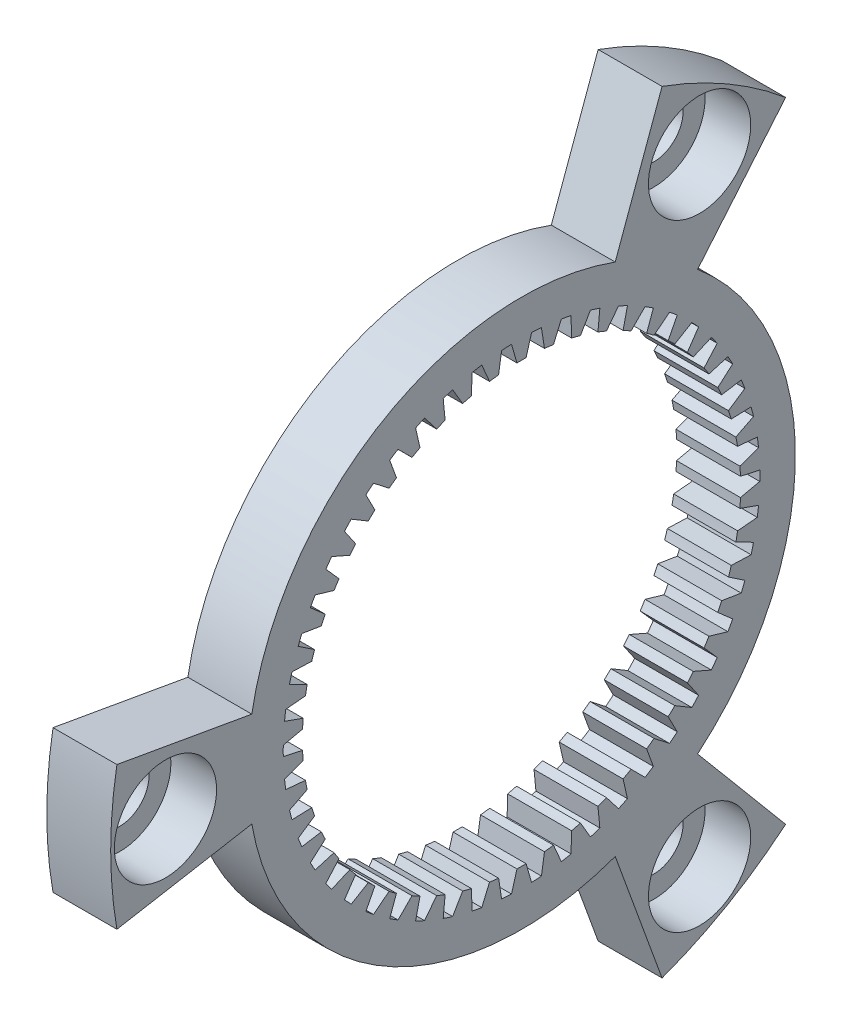
SolidWorks part; units mm, degrees
material "Plain Carbon Steel"
ref_plane "Front Plane" through (0, 0, 0) normal (0, 0, 1) x (1, 0, 0)
ref_plane "Top Plane" through (0, 0, 0) normal (0, 1, 0) x (1, 0, 0)
ref_plane "Right Plane" through (0, 0, 0) normal (1, 0, 0) x (0, 0, -1)
sketch "Sketch1" plane through (0, 0, 0) normal (0, 0, 1) x (1, 0, 0)
  line L0 (-1.5, 22.5) -> (-1.5, 0)
  line L1 (-1.5, 0) -> (2, 0)
  line L2 (2, 0) -> (2, 22.5)
  line L3 (2, 22.5) -> (-1.5, 22.5)
  line L4 (-1.5, 0) -> (2, 0) construction
revolve "Revolve1" add sketch "Sketch1" angle 360 about L4
sketch "Sketch2" plane through (-1.5, 0, 0) normal (-1, 0, 0) x (0, 0, 1)
  line L0 (22.1582, -3.9071) -> (14.7721, -2.6047)
  line L1 (-5.1303, -14.0954) -> (-7.6955, -21.1431)
  arc A0 (-7.6955, -21.1431) -> (22.1582, -3.9071) centre (0, 0) ccw
  arc A1 (14.7721, -2.6047) -> (-5.1303, -14.0954) centre (0, 0) cw
extrude "Cut-Extrude1" cut sketch "Sketch2" against normal through all
sketch "Sketch3" plane through (-1.5, 0, 0) normal (-1, 0, 0) x (0, 0, 1)
  line L0 (-14.4627, -17.236) -> (-9.6418, -11.4907)
  line L1 (-9.6418, 11.4907) -> (-14.4627, 17.236)
  arc A0 (-14.4627, 17.236) -> (-14.4627, -17.236) centre (0, 0) ccw
  arc A1 (-9.6418, -11.4907) -> (-9.6418, 11.4907) centre (0, 0) cw
extrude "Cut-Extrude2" cut sketch "Sketch3" against normal through all
sketch "Sketch4" plane through (-1.5, 0, 0) normal (-1, 0, 0) x (0, 0, 1)
  line L0 (-7.6955, 21.1431) -> (-5.1303, 14.0954)
  line L1 (14.7721, 2.6047) -> (22.1582, 3.9071)
  arc A0 (22.1582, 3.9071) -> (-7.6955, 21.1431) centre (0, 0) ccw
  arc A1 (-5.1303, 14.0954) -> (14.7721, 2.6047) centre (0, 0) cw
extrude "Cut-Extrude3" cut sketch "Sketch4" against normal through all
sketch "Sketch5" plane through (-1.5, 0, 0) normal (-1, 0, 0) x (0, 0, 1)
  line L0 (11.958, 1.0028) -> (12.9782, 1.3667)
  line L1 (12.9104, 1.9038) -> (11.8317, 2.0025)
  line L2 (11.738, 2.4937) -> (12.7046, 2.9825)
  line L3 (12.57, 3.5069) -> (11.4875, 3.4696)
  line L4 (11.3329, 3.9452) -> (12.2306, 4.5513)
  line L5 (12.0313, 5.0546) -> (10.962, 4.882)
  line L6 (10.7491, 5.3344) -> (11.5637, 6.0483)
  line L7 (11.3029, 6.5227) -> (10.2637, 6.2174)
  line L8 (9.9958, 6.6396) -> (10.7145, 7.45)
  line L9 (10.3963, 7.8879) -> (9.4035, 7.4548)
  line L10 (9.0848, 7.8401) -> (9.6963, 8.7341)
  line L11 (9.3257, 9.1287) -> (8.395, 8.5746)
  line L12 (8.0305, 8.9169) -> (8.5251, 9.8805)
  line L13 (8.108, 10.2256) -> (7.2541, 9.5592)
  line L14 (6.8496, 9.853) -> (7.2196, 10.8711)
  line L15 (6.7625, 11.1611) -> (5.9989, 10.393)
  line L16 (5.5607, 10.6338) -> (5.8001, 11.6902)
  line L17 (5.3103, 11.9207) -> (4.649, 11.0629)
  line L18 (4.1841, 11.2469) -> (4.2892, 12.325)
  line L19 (3.7744, 12.4923) -> (3.2258, 11.5583)
  line L20 (2.7415, 11.6826) -> (2.7107, 12.7654)
  line L21 (2.1789, 12.8668) -> (1.7517, 11.8715)
  line L22 (1.2556, 11.9341) -> (1.0894, 13.0045)
  line L23 (0.5491, 13.0384) -> (0.25, 11.9974)
  line L24 (-0.25, 11.9974) -> (-0.5491, 13.0384)
  line L25 (-1.0894, 13.0045) -> (-1.2556, 11.9341)
  line L26 (-1.7517, 11.8715) -> (-2.1789, 12.8668)
  line L27 (-2.7107, 12.7654) -> (-2.7415, 11.6826)
  line L28 (-3.2258, 11.5583) -> (-3.7744, 12.4923)
  line L29 (-4.2892, 12.325) -> (-4.1841, 11.2469)
  line L30 (-4.649, 11.0629) -> (-5.3103, 11.9207)
  line L31 (-5.8001, 11.6902) -> (-5.5607, 10.6338)
  line L32 (-5.9989, 10.393) -> (-6.7625, 11.1611)
  line L33 (-7.2196, 10.8711) -> (-6.8496, 9.853)
  line L34 (-7.2541, 9.5592) -> (-8.108, 10.2256)
  line L35 (-8.5251, 9.8805) -> (-8.0305, 8.9169)
  line L36 (-8.395, 8.5746) -> (-9.3257, 9.1287)
  line L37 (-9.6963, 8.7341) -> (-9.0848, 7.8401)
  line L38 (-9.4035, 7.4548) -> (-10.3963, 7.8879)
  line L39 (-10.7145, 7.45) -> (-9.9958, 6.6396)
  line L40 (-10.2637, 6.2174) -> (-11.3029, 6.5227)
  line L41 (-11.5637, 6.0483) -> (-10.7491, 5.3344)
  line L42 (-10.962, 4.882) -> (-12.0313, 5.0546)
  line L43 (-12.2306, 4.5513) -> (-11.3329, 3.9452)
  line L44 (-11.4875, 3.4696) -> (-12.57, 3.5069)
  line L45 (-12.7046, 2.9825) -> (-11.738, 2.4937)
  line L46 (-11.8317, 2.0025) -> (-12.9104, 1.9038)
  line L47 (-12.9782, 1.3667) -> (-11.958, 1.0028)
  line L48 (-11.9894, 0.5038) -> (-13.0472, 0.2707)
  line L49 (-13.0472, -0.2707) -> (-11.9894, -0.5038)
  line L50 (-11.958, -1.0028) -> (-12.9782, -1.3667)
  line L51 (-12.9104, -1.9038) -> (-11.8317, -2.0025)
  line L52 (-11.738, -2.4937) -> (-12.7046, -2.9825)
  line L53 (-12.57, -3.5069) -> (-11.4875, -3.4696)
  line L54 (-11.3329, -3.9452) -> (-12.2306, -4.5513)
  line L55 (-12.0313, -5.0546) -> (-10.962, -4.882)
  line L56 (-10.7491, -5.3344) -> (-11.5637, -6.0483)
  line L57 (-11.3029, -6.5227) -> (-10.2637, -6.2174)
  line L58 (-9.9958, -6.6396) -> (-10.7145, -7.45)
  line L59 (-10.3963, -7.8879) -> (-9.4035, -7.4548)
  line L60 (-9.0848, -7.8401) -> (-9.6963, -8.7341)
  line L61 (-9.3257, -9.1287) -> (-8.395, -8.5746)
  line L62 (-8.0305, -8.9169) -> (-8.5251, -9.8805)
  line L63 (-8.108, -10.2256) -> (-7.2541, -9.5592)
  line L64 (-6.8496, -9.853) -> (-7.2196, -10.8711)
  line L65 (-6.7625, -11.1611) -> (-5.9989, -10.393)
  line L66 (-5.5607, -10.6338) -> (-5.8001, -11.6902)
  line L67 (-5.3103, -11.9207) -> (-4.649, -11.0629)
  line L68 (-4.1841, -11.2469) -> (-4.2892, -12.325)
  line L69 (-3.7744, -12.4923) -> (-3.2258, -11.5583)
  line L70 (-2.7415, -11.6826) -> (-2.7107, -12.7654)
  line L71 (-2.1789, -12.8668) -> (-1.7517, -11.8715)
  line L72 (-1.2556, -11.9341) -> (-1.0894, -13.0045)
  line L73 (-0.5491, -13.0384) -> (-0.25, -11.9974)
  line L74 (0.25, -11.9974) -> (0.5491, -13.0384)
  line L75 (1.0894, -13.0045) -> (1.2556, -11.9341)
  line L76 (1.7517, -11.8715) -> (2.1789, -12.8668)
  line L77 (2.7107, -12.7654) -> (2.7415, -11.6826)
  line L78 (3.2258, -11.5583) -> (3.7744, -12.4923)
  line L79 (4.2892, -12.325) -> (4.1841, -11.2469)
  line L80 (4.649, -11.0629) -> (5.3103, -11.9207)
  line L81 (5.8001, -11.6902) -> (5.5607, -10.6338)
  line L82 (5.9989, -10.393) -> (6.7625, -11.1611)
  line L83 (7.2196, -10.8711) -> (6.8496, -9.853)
  line L84 (7.2541, -9.5592) -> (8.108, -10.2256)
  line L85 (8.5251, -9.8805) -> (8.0305, -8.9169)
  line L86 (8.395, -8.5746) -> (9.3257, -9.1287)
  line L87 (9.6963, -8.7341) -> (9.0848, -7.8401)
  line L88 (9.4035, -7.4548) -> (10.3963, -7.8879)
  line L89 (10.7145, -7.45) -> (9.9958, -6.6396)
  line L90 (10.2637, -6.2174) -> (11.3029, -6.5227)
  line L91 (11.5637, -6.0483) -> (10.7491, -5.3344)
  line L92 (10.962, -4.882) -> (12.0313, -5.0546)
  line L93 (12.2306, -4.5513) -> (11.3329, -3.9452)
  line L94 (11.4875, -3.4696) -> (12.57, -3.5069)
  line L95 (12.7046, -2.9825) -> (11.738, -2.4937)
  line L96 (11.8317, -2.0025) -> (12.9104, -1.9038)
  line L97 (12.9782, -1.3667) -> (11.958, -1.0028)
  line L98 (11.9894, -0.5038) -> (13.0472, -0.2707)
  line L99 (13.0472, 0.2707) -> (11.9894, 0.5038)
  arc A0 (12.9782, 1.3667) -> (12.9104, 1.9038) centre (0, 0) ccw
  arc A1 (11.8317, 2.0025) -> (11.738, 2.4937) centre (0, 0) ccw
  arc A2 (12.7046, 2.9825) -> (12.57, 3.5069) centre (0, 0) ccw
  arc A3 (11.4875, 3.4696) -> (11.3329, 3.9452) centre (0, 0) ccw
  arc A4 (12.2306, 4.5513) -> (12.0313, 5.0546) centre (0, 0) ccw
  arc A5 (10.962, 4.882) -> (10.7491, 5.3344) centre (0, 0) ccw
  arc A6 (11.5637, 6.0483) -> (11.3029, 6.5227) centre (0, 0) ccw
  arc A7 (10.2637, 6.2174) -> (9.9958, 6.6396) centre (0, 0) ccw
  arc A8 (10.7145, 7.45) -> (10.3963, 7.8879) centre (0, 0) ccw
  arc A9 (9.4035, 7.4548) -> (9.0848, 7.8401) centre (0, 0) ccw
  arc A10 (9.6963, 8.7341) -> (9.3257, 9.1287) centre (0, 0) ccw
  arc A11 (8.395, 8.5746) -> (8.0305, 8.9169) centre (0, 0) ccw
  arc A12 (8.5251, 9.8805) -> (8.108, 10.2256) centre (0, 0) ccw
  arc A13 (7.2541, 9.5592) -> (6.8496, 9.853) centre (0, 0) ccw
  arc A14 (7.2196, 10.8711) -> (6.7625, 11.1611) centre (0, 0) ccw
  arc A15 (5.9989, 10.393) -> (5.5607, 10.6338) centre (0, 0) ccw
  arc A16 (5.8001, 11.6902) -> (5.3103, 11.9207) centre (0, 0) ccw
  arc A17 (4.649, 11.0629) -> (4.1841, 11.2469) centre (0, 0) ccw
  arc A18 (4.2892, 12.325) -> (3.7744, 12.4923) centre (0, 0) ccw
  arc A19 (3.2258, 11.5583) -> (2.7415, 11.6826) centre (0, 0) ccw
  arc A20 (2.7107, 12.7654) -> (2.1789, 12.8668) centre (0, 0) ccw
  arc A21 (1.7517, 11.8715) -> (1.2556, 11.9341) centre (0, 0) ccw
  arc A22 (1.0894, 13.0045) -> (0.5491, 13.0384) centre (0, 0) ccw
  arc A23 (0.25, 11.9974) -> (-0.25, 11.9974) centre (0, 0) ccw
  arc A24 (-0.5491, 13.0384) -> (-1.0894, 13.0045) centre (0, 0) ccw
  arc A25 (-1.2556, 11.9341) -> (-1.7517, 11.8715) centre (0, 0) ccw
  arc A26 (-2.1789, 12.8668) -> (-2.7107, 12.7654) centre (0, 0) ccw
  arc A27 (-2.7415, 11.6826) -> (-3.2258, 11.5583) centre (0, 0) ccw
  arc A28 (-3.7744, 12.4923) -> (-4.2892, 12.325) centre (0, 0) ccw
  arc A29 (-4.1841, 11.2469) -> (-4.649, 11.0629) centre (0, 0) ccw
  arc A30 (-5.3103, 11.9207) -> (-5.8001, 11.6902) centre (0, 0) ccw
  arc A31 (-5.5607, 10.6338) -> (-5.9989, 10.393) centre (0, 0) ccw
  arc A32 (-6.7625, 11.1611) -> (-7.2196, 10.8711) centre (0, 0) ccw
  arc A33 (-6.8496, 9.853) -> (-7.2541, 9.5592) centre (0, 0) ccw
  arc A34 (-8.108, 10.2256) -> (-8.5251, 9.8805) centre (0, 0) ccw
  arc A35 (-8.0305, 8.9169) -> (-8.395, 8.5746) centre (0, 0) ccw
  arc A36 (-9.3257, 9.1287) -> (-9.6963, 8.7341) centre (0, 0) ccw
  arc A37 (-9.0848, 7.8401) -> (-9.4035, 7.4548) centre (0, 0) ccw
  arc A38 (-10.3963, 7.8879) -> (-10.7145, 7.45) centre (0, 0) ccw
  arc A39 (-9.9958, 6.6396) -> (-10.2637, 6.2174) centre (0, 0) ccw
  arc A40 (-11.3029, 6.5227) -> (-11.5637, 6.0483) centre (0, 0) ccw
  arc A41 (-10.7491, 5.3344) -> (-10.962, 4.882) centre (0, 0) ccw
  arc A42 (-12.0313, 5.0546) -> (-12.2306, 4.5513) centre (0, 0) ccw
  arc A43 (-11.3329, 3.9452) -> (-11.4875, 3.4696) centre (0, 0) ccw
  arc A44 (-12.57, 3.5069) -> (-12.7046, 2.9825) centre (0, 0) ccw
  arc A45 (-11.738, 2.4937) -> (-11.8317, 2.0025) centre (0, 0) ccw
  arc A46 (-12.9104, 1.9038) -> (-12.9782, 1.3667) centre (0, 0) ccw
  arc A47 (-11.958, 1.0028) -> (-11.9894, 0.5038) centre (0, 0) ccw
  arc A48 (-13.0472, 0.2707) -> (-13.0472, -0.2707) centre (0, 0) ccw
  arc A49 (-11.9894, -0.5038) -> (-11.958, -1.0028) centre (0, 0) ccw
  arc A50 (-12.9782, -1.3667) -> (-12.9104, -1.9038) centre (0, 0) ccw
  arc A51 (-11.8317, -2.0025) -> (-11.738, -2.4937) centre (0, 0) ccw
  arc A52 (-12.7046, -2.9825) -> (-12.57, -3.5069) centre (0, 0) ccw
  arc A53 (-11.4875, -3.4696) -> (-11.3329, -3.9452) centre (0, 0) ccw
  arc A54 (-12.2306, -4.5513) -> (-12.0313, -5.0546) centre (0, 0) ccw
  arc A55 (-10.962, -4.882) -> (-10.7491, -5.3344) centre (0, 0) ccw
  arc A56 (-11.5637, -6.0483) -> (-11.3029, -6.5227) centre (0, 0) ccw
  arc A57 (-10.2637, -6.2174) -> (-9.9958, -6.6396) centre (0, 0) ccw
  arc A58 (-10.7145, -7.45) -> (-10.3963, -7.8879) centre (0, 0) ccw
  arc A59 (-9.4035, -7.4548) -> (-9.0848, -7.8401) centre (0, 0) ccw
  arc A60 (-9.6963, -8.7341) -> (-9.3257, -9.1287) centre (0, 0) ccw
  arc A61 (-8.395, -8.5746) -> (-8.0305, -8.9169) centre (0, 0) ccw
  arc A62 (-8.5251, -9.8805) -> (-8.108, -10.2256) centre (0, 0) ccw
  arc A63 (-7.2541, -9.5592) -> (-6.8496, -9.853) centre (0, 0) ccw
  arc A64 (-7.2196, -10.8711) -> (-6.7625, -11.1611) centre (0, 0) ccw
  arc A65 (-5.9989, -10.393) -> (-5.5607, -10.6338) centre (0, 0) ccw
  arc A66 (-5.8001, -11.6902) -> (-5.3103, -11.9207) centre (0, 0) ccw
  arc A67 (-4.649, -11.0629) -> (-4.1841, -11.2469) centre (0, 0) ccw
  arc A68 (-4.2892, -12.325) -> (-3.7744, -12.4923) centre (0, 0) ccw
  arc A69 (-3.2258, -11.5583) -> (-2.7415, -11.6826) centre (0, 0) ccw
  arc A70 (-2.7107, -12.7654) -> (-2.1789, -12.8668) centre (0, 0) ccw
  arc A71 (-1.7517, -11.8715) -> (-1.2556, -11.9341) centre (0, 0) ccw
  arc A72 (-1.0894, -13.0045) -> (-0.5491, -13.0384) centre (0, 0) ccw
  arc A73 (-0.25, -11.9974) -> (0.25, -11.9974) centre (0, 0) ccw
  arc A74 (0.5491, -13.0384) -> (1.0894, -13.0045) centre (0, 0) ccw
  arc A75 (1.2556, -11.9341) -> (1.7517, -11.8715) centre (0, 0) ccw
  arc A76 (2.1789, -12.8668) -> (2.7107, -12.7654) centre (0, 0) ccw
  arc A77 (2.7415, -11.6826) -> (3.2258, -11.5583) centre (0, 0) ccw
  arc A78 (3.7744, -12.4923) -> (4.2892, -12.325) centre (0, 0) ccw
  arc A79 (4.1841, -11.2469) -> (4.649, -11.0629) centre (0, 0) ccw
  arc A80 (5.3103, -11.9207) -> (5.8001, -11.6902) centre (0, 0) ccw
  arc A81 (5.5607, -10.6338) -> (5.9989, -10.393) centre (0, 0) ccw
  arc A82 (6.7625, -11.1611) -> (7.2196, -10.8711) centre (0, 0) ccw
  arc A83 (6.8496, -9.853) -> (7.2541, -9.5592) centre (0, 0) ccw
  arc A84 (8.108, -10.2256) -> (8.5251, -9.8805) centre (0, 0) ccw
  arc A85 (8.0305, -8.9169) -> (8.395, -8.5746) centre (0, 0) ccw
  arc A86 (9.3257, -9.1287) -> (9.6963, -8.7341) centre (0, 0) ccw
  arc A87 (9.0848, -7.8401) -> (9.4035, -7.4548) centre (0, 0) ccw
  arc A88 (10.3963, -7.8879) -> (10.7145, -7.45) centre (0, 0) ccw
  arc A89 (9.9958, -6.6396) -> (10.2637, -6.2174) centre (0, 0) ccw
  arc A90 (11.3029, -6.5227) -> (11.5637, -6.0483) centre (0, 0) ccw
  arc A91 (10.7491, -5.3344) -> (10.962, -4.882) centre (0, 0) ccw
  arc A92 (12.0313, -5.0546) -> (12.2306, -4.5513) centre (0, 0) ccw
  arc A93 (11.3329, -3.9452) -> (11.4875, -3.4696) centre (0, 0) ccw
  arc A94 (12.57, -3.5069) -> (12.7046, -2.9825) centre (0, 0) ccw
  arc A95 (11.738, -2.4937) -> (11.8317, -2.0025) centre (0, 0) ccw
  arc A96 (12.9104, -1.9038) -> (12.9782, -1.3667) centre (0, 0) ccw
  arc A97 (11.958, -1.0028) -> (11.9894, -0.5038) centre (0, 0) ccw
  arc A98 (13.0472, -0.2707) -> (13.0472, 0.2707) centre (0, 0) ccw
  arc A99 (11.9894, 0.5038) -> (11.958, 1.0028) centre (0, 0) ccw
extrude "Cut-Extrude4" cut sketch "Sketch5" against normal through all
hole_wizard "CBORE for M3 Hex Head Machine Screw1" positions "Sketch7" profile "Sketch6" counterbore size "M3" standard "ANSI Metric" end condition through all
sketch "Sketch7" plane through (2, 0, 0) normal (1, 0, 0) x (0, 0, -1)
  point P0 (9.75, -16.8875)
  point P1 (-19.5, 0)
  point P2 (9.75, 16.8875)
sketch "Sketch6" plane through (2, -16.8875, -9.75) normal (0, 1, 0) x (0, 0, -1)
  line L0 (0, 0) -> (0, 3.5)
  line L1 (0, 3.5) -> (1.6, 3.5)
  line L3 (1.6, 3.5) -> (1.6, 2.5)
  line L4 (1.6, 2.5) -> (2.8, 2.5)
  line L5 (2.8, 2.5) -> (2.8, 0)
  line L7 (2.8, 0) -> (0, 0)
  line L11 (0, -6.35) -> (0, 107.95) construction
  dimension "Thru Hole Dia." = 3.2
  dimension "Thru Hole Depth" = 3.5
  dimension "C'Bore Dia." = 5.6
  dimension "C'Bore Depth" = 2.5
